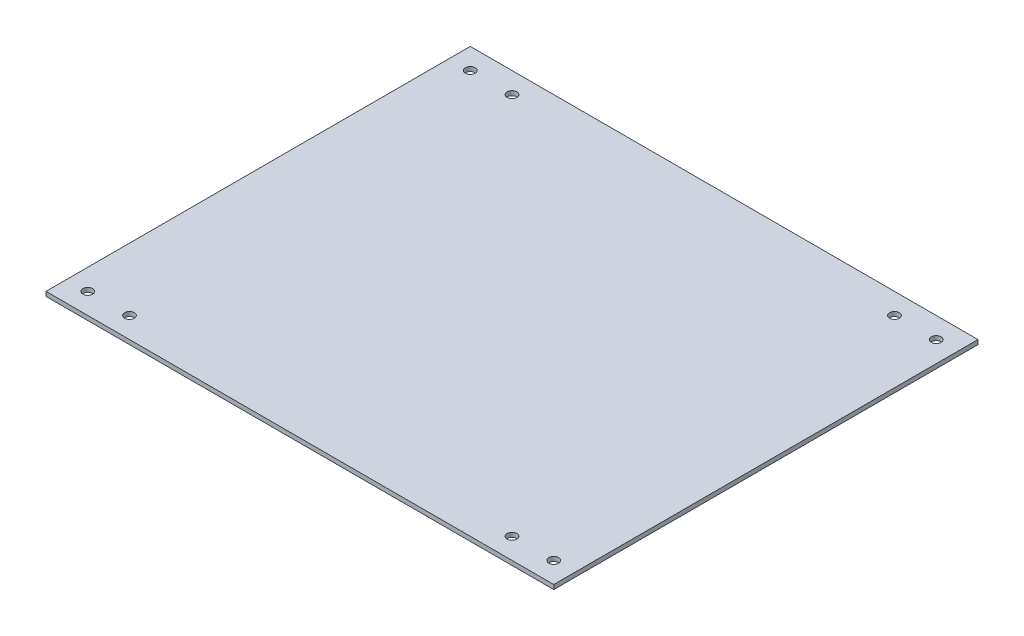
SolidWorks part; units mm, degrees
material "Acrylic (Medium-high impact)"
ref_plane "Front Plane" through (0, 0, 0) normal (0, 0, 1) x (1, 0, 0)
ref_plane "Top Plane" through (0, 0, 0) normal (0, 1, 0) x (1, 0, 0)
ref_plane "Right Plane" through (0, 0, 0) normal (1, 0, 0) x (0, 0, -1)
sketch "Sketch1" plane through (0, 0, 0) normal (0, 1, 0) x (1, 0, 0)
  line L1 (0, 0) -> (364.8, 0)
  line L2 (0, 0) -> (0, 304.8)
  line L3 (0, 304.8) -> (364.8, 304.8)
  line L4 (364.8, 0) -> (364.8, 304.8)
  dimension "D1" = 304.8
  dimension "D2" = 364.8
extrude "Boss-Extrude1" add sketch "Sketch1" along normal blind 3.175
sketch "Sketch4" plane through (0, 3.175, 0) normal (0, 1, 0) x (1, 0, 0)
  line L0 (349.8, 289.8) -> (15, 289.8) construction
  line L1 (15, 289.8) -> (15, 15) construction
  line L2 (15, 15) -> (349.8, 15) construction
  line L3 (349.8, 15) -> (349.8, 289.8) construction
  line L4 (0, 304.8) -> (0, 0)
  line L5 (0, 0) -> (364.8, 0)
  line L6 (364.8, 0) -> (364.8, 304.8)
  line L7 (364.8, 304.8) -> (0, 304.8)
  line L8 (0, 304.8) -> (0, 0) construction
  line L9 (0, 0) -> (364.8, 0) construction
  line L10 (364.8, 0) -> (364.8, 304.8) construction
  line L11 (364.8, 304.8) -> (0, 304.8) construction
  line L16 (45, 289.8) -> (45, 15) construction
  line L18 (319.8, 289.8) -> (319.8, 15) construction
  point P9 (15, 289.8)
  point P10 (349.8, 289.8)
  point P11 (349.8, 15)
  point P12 (15, 15)
  point P40 (45, 289.8)
  point P42 (319.8, 289.8)
  point P44 (319.8, 15)
  point P46 (45, 15)
  dimension "D3" = 30
  dimension "D4" = 30
  dimension "D1" = 0
  dimension "D2" = 15
hole_wizard "Hole1" positions "Sketch4" profile "Sketch6" legacy end condition through all
sketch "Sketch6" plane through (45, 3.175, -15) normal (1, 0, 0) x (0, 0, 1)
  line L0 (0, 0) -> (0, 3.175)
  line L1 (0, 3.175) -> (3.5, 3.175)
  line L2 (3.5, 3.175) -> (3.5, 0)
  line L3 (3.5, 0) -> (0, 0)
  line L4 (0, 110) -> (0, -10) construction
  dimension "Diameter" = 7
  dimension "Depth" = 3.175
